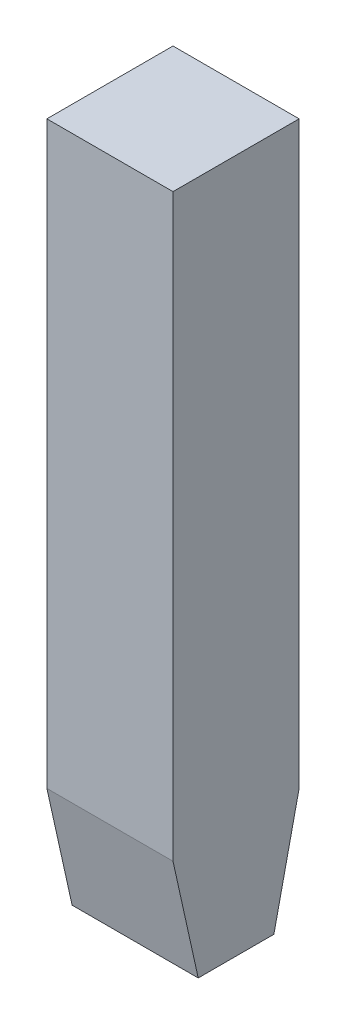
SolidWorks part; units mm, degrees
material "Acier non allié"
ref_plane "Plan de face" through (0, 0, 0) normal (0, 0, 1) x (1, 0, 0)
ref_plane "Plan de dessus" through (0, 0, 0) normal (0, 1, 0) x (1, 0, 0)
ref_plane "Plan de droite" through (0, 0, 0) normal (1, 0, 0) x (0, 0, -1)
sketch "Esquisse1" plane through (0, 0, 0) normal (0, 0, 1) x (1, 0, 0)
  line L0 (-5, 0) -> (5, 0)
other "Elément mécano-soudé1"
ref_plane "Plan1" through (-5, 0, 0) normal (1, 0, 0) x (0, 1, 0)
sketch "plat" plane through (-5, 0, 0) normal (1, 0, 0) x (0, 1, 0)
  line L0 (-27.5, 0) -> (27.5, 0) construction
  line L1 (-27.5, 5) -> (27.5, 5)
  line L2 (-27.5, 5) -> (-27.5, -5)
  line L3 (-27.5, -5) -> (27.5, -5)
  line L4 (27.5, 5) -> (27.5, -5)
  line L5 (0, 5) -> (0, -5) construction
  point P8 (0, 0)
  dimension "B" = 55
  dimension "A" = 10
sketch "Esquisse2" plane through (0, 0, 0) normal (1, 0, 0) x (0, 0, -1)
  line L0 (-3, -27.5) -> (-5, -18.4786)
  line L1 (-5, -27.5) -> (5, -27.5) construction
  line L2 (-5, 27.5) -> (-5, -27.5) construction
  line L3 (-5, -18.4786) -> (-5, -27.5)
  line L4 (-5, -27.5) -> (-3, -27.5)
  line L5 (5, -27.5) -> (5, -18.4786)
  line L6 (5, -27.5) -> (5, 27.5) construction
  line L7 (5, -18.4786) -> (3, -27.5)
  line L8 (3, -27.5) -> (5, -27.5)
  dimension "D1" = 6
  dimension "D2" = 25
  dimension "D3" = 9.0214
extrude "Enlèv. mat.-Extru.1" cut sketch "Esquisse2" against normal through all both and the other way through all
sketch "Esquisse3" plane through (0, 27.5, 0) normal (0, 1, 0) x (1, 0, 0)
  line L0 (5, 5) -> (5, -5) construction
  circle A0 centre (0, 0) radius 5
extrude "Enlèv. mat.-Extru.2" [suppressed] cut sketch "Esquisse3" against normal blind 10 flip side to cut
